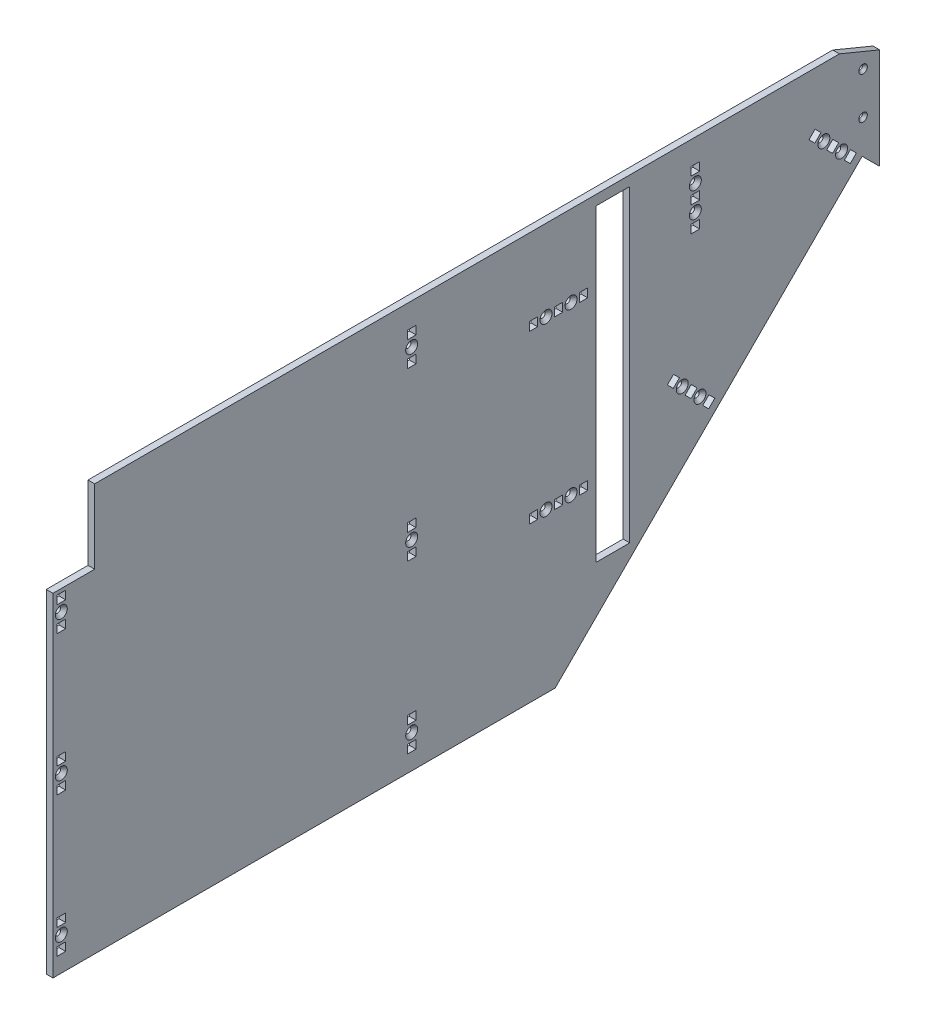
SolidWorks part; units mm, degrees
material "Delrin 2700 NC010, Low Viscosity Acetal Copolymer (SS)"
ref_plane "Front Plane" through (0, 0, 0) normal (0, 0, 1) x (1, 0, 0)
ref_plane "Top Plane" through (0, 0, 0) normal (0, 1, 0) x (1, 0, 0)
ref_plane "Right Plane" through (0, 0, 0) normal (1, 0, 0) x (0, 0, -1)
sketch "Sketch1" plane through (0, 0, 0) normal (1, 0, 0) x (0, 0, -1)
  line L0 (307.975, 0) -> (307.975, -76.2) construction
  line L1 (-307.975, 0) -> (307.975, 0)
  line L2 (-307.975, 0) -> (-307.975, -309.88)
  line L3 (-307.975, -309.88) -> (74.295, -309.88)
  line L4 (101.6, -254) -> (-228.6, -254) construction
  line L5 (105.41, -7.62) -> (131.064, -7.62)
  line L6 (105.41, -7.62) -> (105.41, -242.57)
  line L7 (307.975, -76.2) -> (74.295, -309.88)
  line L8 (105.41, -242.57) -> (131.064, -242.57)
  line L9 (131.064, -7.62) -> (131.064, -242.57)
  line L10 (101.6, -254) -> (101.6, 0) construction
  line L11 (-228.6, -254) -> (-228.6, 0) construction
  line L12 (-307.975, -5.08) -> (307.975, -5.08) construction
  line L13 (101.6, -254) -> (130.175, -254) construction
  line L14 (307.975, -76.2) -> (307.975, -289.8019) construction
  line L15 (307.975, -76.2) -> (321.3376, -89.5626)
  line L17 (321.3376, -89.5626) -> (321.3376, 0)
  line L18 (321.3376, 0) -> (307.975, 0)
  point P0 (0, 0)
  dimension "D1" = 234.95
  dimension "D2" = 25.654
  dimension "D3" = 45
  dimension "D4" = 304.8
  dimension "D5" = 254
  dimension "D6" = 76.2
  dimension "D7" = 330.2
  dimension "D8" = 5.08
  dimension "D9" = 2.54
  dimension "D10" = 3.81
  dimension "D11" = 79.375
  dimension "D12" = 615.95
  dimension "D13" = 251.4472
  dimension "D14" = 18.8976
  dimension "D15" = 7.4536
extrude "Boss-Extrude1" add sketch "Sketch1" along normal blind 5.08
sketch "Sketch2" plane through (5.08, 0, 0) normal (1, 0, 0) x (0, 0, -1)
  line L1 (-307.975, 0) -> (-276.225, 0)
  line L2 (-307.975, 0) -> (-307.975, -56.261)
  line L3 (-307.975, -56.261) -> (-276.225, -56.261)
  line L4 (-276.225, 0) -> (-276.225, -56.261)
  dimension "D1" = 31.75
  dimension "D2" = 56.261
extrude "Cut-Extrude1" cut sketch "Sketch2" against normal through all
chamfer "Chamfer1" distance 12.7 angle 67.5 1 edges at (2.54, 0, -321.3376)
sketch "Sketch4" plane through (5.08, 0, 0) normal (1, 0, 0) x (0, 0, -1)
  line L6 (307.975, -76.2) -> (321.3376, -89.5626) construction
  line L7 (74.295, -309.88) -> (307.975, -76.2) construction
  line B0 (285.6142, -53.8392) -> (290.1043, -58.3293)
  line B1 (290.1043, -58.3293) -> (285.4346, -62.999)
  line B2 (285.4346, -62.999) -> (280.9444, -58.5089)
  line B3 (280.9444, -58.5089) -> (285.6142, -53.8392)
  line B4 (272.1438, -40.3688) -> (276.6339, -44.8589)
  line B5 (276.6339, -44.8589) -> (271.9642, -49.5286)
  line B6 (271.9642, -49.5286) -> (267.474, -45.0385)
  line B7 (267.474, -45.0385) -> (272.1438, -40.3688)
  circle B8 centre (278.7892, -51.6839) radius 2.1526
  line B9 (299.0845, -67.3095) -> (303.5747, -71.7997)
  line B10 (299.0845, -67.3095) -> (294.4148, -71.9793)
  line B11 (294.4148, -71.9793) -> (298.9049, -76.4694)
  line B12 (303.5747, -71.7997) -> (298.9049, -76.4694)
  circle B13 centre (292.2596, -65.1543) radius 2.1527
  line B14 (177.8511, -161.6022) -> (182.3412, -166.0924)
  line B15 (182.3412, -166.0924) -> (177.6715, -170.7621)
  line B16 (177.6715, -170.7621) -> (173.1814, -166.272)
  line B17 (173.1814, -166.272) -> (177.8511, -161.6022)
  line B18 (164.3807, -148.1319) -> (168.8708, -152.622)
  line B19 (168.8708, -152.622) -> (164.2011, -157.2917)
  line B20 (164.2011, -157.2917) -> (159.711, -152.8016)
  line B21 (159.711, -152.8016) -> (164.3807, -148.1319)
  circle B22 centre (171.0261, -159.447) radius 2.1526
  line B23 (191.3215, -175.0726) -> (195.8116, -179.5627)
  line B24 (191.3215, -175.0726) -> (186.6517, -179.7424)
  line B25 (186.6517, -179.7424) -> (191.1419, -184.2325)
  line B26 (195.8116, -179.5627) -> (191.1419, -184.2325)
  circle B27 centre (184.4965, -172.9174) radius 2.1527
  dimension "D1" = 152.4
  dimension "D2" = 6.223
sketch_block_instance "BOLT_HOLE_2X-6"
sketch_block "BOLT_HOLE_2X" parameters "D1"=4.3053, "D2"=6.35, "D3"=6.35, "D4"=6.604, "D5"=19.05
sketch_block_instance "BOLT_HOLE_2X-7"
extrude "Cut-Extrude5" cut sketch "Sketch4" against normal through all
sketch "Sketch5" plane through (5.08, 0, 0) normal (1, 0, 0) x (0, 0, -1)
  line L0 (105.41, -7.62) -> (105.41, -242.57) construction
  line L3 (131.064, -7.62) -> (105.41, -7.62) construction
  line B0 (73.66, -58.42) -> (80.01, -58.42)
  line B1 (80.01, -58.42) -> (80.01, -65.024)
  line B2 (80.01, -65.024) -> (73.66, -65.024)
  line B3 (73.66, -65.024) -> (73.66, -58.42)
  line B4 (54.61, -58.42) -> (60.96, -58.42)
  line B5 (60.96, -58.42) -> (60.96, -65.024)
  line B6 (60.96, -65.024) -> (54.61, -65.024)
  line B7 (54.61, -65.024) -> (54.61, -58.42)
  circle B8 centre (67.31, -61.722) radius 2.1526
  line B9 (67.31, -61.722) -> (60.96, -61.722) construction
  line B10 (67.31, -61.722) -> (73.66, -61.722) construction
  line B11 (80.01, -61.722) -> (86.36, -61.722) construction
  line B12 (92.71, -58.42) -> (99.06, -58.42)
  line B13 (92.71, -58.42) -> (92.71, -65.024)
  line B14 (92.71, -65.024) -> (99.06, -65.024)
  line B15 (99.06, -58.42) -> (99.06, -65.024)
  line B16 (86.36, -61.722) -> (92.71, -61.722) construction
  circle B17 centre (86.36, -61.722) radius 2.1527
  line B18 (73.66, -185.42) -> (80.01, -185.42)
  line B19 (80.01, -185.42) -> (80.01, -192.024)
  line B20 (80.01, -192.024) -> (73.66, -192.024)
  line B21 (73.66, -192.024) -> (73.66, -185.42)
  line B22 (54.61, -185.42) -> (60.96, -185.42)
  line B23 (60.96, -185.42) -> (60.96, -192.024)
  line B24 (60.96, -192.024) -> (54.61, -192.024)
  line B25 (54.61, -192.024) -> (54.61, -185.42)
  circle B26 centre (67.31, -188.722) radius 2.1526
  line B27 (67.31, -188.722) -> (60.96, -188.722) construction
  line B28 (67.31, -188.722) -> (73.66, -188.722) construction
  line B29 (80.01, -188.722) -> (86.36, -188.722) construction
  line B30 (92.71, -185.42) -> (99.06, -185.42)
  line B31 (92.71, -185.42) -> (92.71, -192.024)
  line B32 (92.71, -192.024) -> (99.06, -192.024)
  line B33 (99.06, -185.42) -> (99.06, -192.024)
  line B34 (86.36, -188.722) -> (92.71, -188.722) construction
  circle B35 centre (86.36, -188.722) radius 2.1527
  dimension "D1" = 6.35
  dimension "D2" = 50.8
  dimension "D3" = 127
sketch_block_instance "BOLT_HOLE_2X-1"
sketch_block_instance "BOLT_HOLE_2X-2"
extrude "Cut-Extrude6" cut sketch "Sketch5" against normal through all
sketch "Sketch6" plane through (5.08, 0, 0) normal (1, 0, 0) x (0, 0, -1)
  line L0 (-301.625, -71.755) -> (-301.625, -178.1175) construction
  line L1 (-301.625, -178.1175) -> (-301.625, -284.48) construction
  line L2 (-34.925, -30.48) -> (-34.925, -157.48) construction
  line L3 (-34.925, -157.48) -> (-34.925, -284.48) construction
  line L4 (-307.975, -309.88) -> (74.295, -309.88) construction
  line L5 (-307.975, -56.261) -> (-307.975, -309.88) construction
  line L7 (290.6771, 0) -> (-276.225, 0) construction
  line B0 (184.277, -36.83) -> (184.277, -43.18)
  line B1 (184.277, -43.18) -> (177.673, -43.18)
  line B2 (177.673, -43.18) -> (177.673, -36.83)
  line B3 (177.673, -36.83) -> (184.277, -36.83)
  line B4 (184.277, -17.78) -> (184.277, -24.13)
  line B5 (184.277, -24.13) -> (177.673, -24.13)
  line B6 (177.673, -24.13) -> (177.673, -17.78)
  line B7 (177.673, -17.78) -> (184.277, -17.78)
  circle B8 centre (180.975, -30.48) radius 2.1526
  line B9 (180.975, -30.48) -> (180.975, -24.13) construction
  line B10 (180.975, -30.48) -> (180.975, -36.83) construction
  line B11 (180.975, -43.18) -> (180.975, -49.53) construction
  line B12 (184.277, -55.88) -> (184.277, -62.23)
  line B13 (184.277, -55.88) -> (177.673, -55.88)
  line B14 (177.673, -55.88) -> (177.673, -62.23)
  line B15 (184.277, -62.23) -> (177.673, -62.23)
  line B16 (180.975, -49.53) -> (180.975, -55.88) construction
  circle B17 centre (180.975, -49.53) radius 2.1527
  line B18 (-31.623, -290.83) -> (-31.623, -297.18)
  line B19 (-31.623, -297.18) -> (-38.227, -297.18)
  line B20 (-38.227, -297.18) -> (-38.227, -290.83)
  line B21 (-38.227, -290.83) -> (-31.623, -290.83)
  line B22 (-31.623, -271.78) -> (-31.623, -278.13)
  line B23 (-31.623, -278.13) -> (-38.227, -278.13)
  line B24 (-38.227, -278.13) -> (-38.227, -271.78)
  line B25 (-38.227, -271.78) -> (-31.623, -271.78)
  circle B26 centre (-34.925, -284.48) radius 2.1526
  line B27 (-34.925, -284.48) -> (-34.925, -278.13) construction
  line B28 (-34.925, -284.48) -> (-34.925, -290.83) construction
  line B29 (-31.623, -36.83) -> (-31.623, -43.18)
  line B30 (-31.623, -43.18) -> (-38.227, -43.18)
  line B31 (-38.227, -43.18) -> (-38.227, -36.83)
  line B32 (-38.227, -36.83) -> (-31.623, -36.83)
  line B33 (-31.623, -17.78) -> (-31.623, -24.13)
  line B34 (-31.623, -24.13) -> (-38.227, -24.13)
  line B35 (-38.227, -24.13) -> (-38.227, -17.78)
  line B36 (-38.227, -17.78) -> (-31.623, -17.78)
  circle B37 centre (-34.925, -30.48) radius 2.1526
  line B38 (-34.925, -30.48) -> (-34.925, -24.13) construction
  line B39 (-34.925, -30.48) -> (-34.925, -36.83) construction
  line B40 (-38.227, -151.13) -> (-38.227, -144.78)
  line B41 (-38.227, -144.78) -> (-31.623, -144.78)
  line B42 (-31.623, -144.78) -> (-31.623, -151.13)
  line B43 (-31.623, -151.13) -> (-38.227, -151.13)
  line B44 (-38.227, -170.18) -> (-38.227, -163.83)
  line B45 (-38.227, -163.83) -> (-31.623, -163.83)
  line B46 (-31.623, -163.83) -> (-31.623, -170.18)
  line B47 (-31.623, -170.18) -> (-38.227, -170.18)
  circle B48 centre (-34.925, -157.48) radius 2.1526
  line B49 (-34.925, -157.48) -> (-34.925, -163.83) construction
  line B50 (-34.925, -157.48) -> (-34.925, -151.13) construction
  line B51 (-304.927, -65.405) -> (-304.927, -59.055)
  line B52 (-304.927, -59.055) -> (-298.323, -59.055)
  line B53 (-298.323, -59.055) -> (-298.323, -65.405)
  line B54 (-298.323, -65.405) -> (-304.927, -65.405)
  line B55 (-304.927, -84.455) -> (-304.927, -78.105)
  line B56 (-304.927, -78.105) -> (-298.323, -78.105)
  line B57 (-298.323, -78.105) -> (-298.323, -84.455)
  line B58 (-298.323, -84.455) -> (-304.927, -84.455)
  circle B59 centre (-301.625, -71.755) radius 2.1526
  line B60 (-301.625, -71.755) -> (-301.625, -78.105) construction
  line B61 (-301.625, -71.755) -> (-301.625, -65.405) construction
  line B62 (-304.927, -171.7675) -> (-304.927, -165.4175)
  line B63 (-304.927, -165.4175) -> (-298.323, -165.4175)
  line B64 (-298.323, -165.4175) -> (-298.323, -171.7675)
  line B65 (-298.323, -171.7675) -> (-304.927, -171.7675)
  line B66 (-304.927, -190.8175) -> (-304.927, -184.4675)
  line B67 (-304.927, -184.4675) -> (-298.323, -184.4675)
  line B68 (-298.323, -184.4675) -> (-298.323, -190.8175)
  line B69 (-298.323, -190.8175) -> (-304.927, -190.8175)
  circle B70 centre (-301.625, -178.1175) radius 2.1526
  line B71 (-301.625, -178.1175) -> (-301.625, -184.4675) construction
  line B72 (-301.625, -178.1175) -> (-301.625, -171.7675) construction
  line B73 (-304.927, -278.13) -> (-304.927, -271.78)
  line B74 (-304.927, -271.78) -> (-298.323, -271.78)
  line B75 (-298.323, -271.78) -> (-298.323, -278.13)
  line B76 (-298.323, -278.13) -> (-304.927, -278.13)
  line B77 (-304.927, -297.18) -> (-304.927, -290.83)
  line B78 (-304.927, -290.83) -> (-298.323, -290.83)
  line B79 (-298.323, -290.83) -> (-298.323, -297.18)
  line B80 (-298.323, -297.18) -> (-304.927, -297.18)
  circle B81 centre (-301.625, -284.48) radius 2.1526
  line B82 (-301.625, -284.48) -> (-301.625, -290.83) construction
  line B83 (-301.625, -284.48) -> (-301.625, -278.13) construction
  dimension "D1" = 266.7
  dimension "D2" = 59.055
  dimension "D3" = 12.7
  dimension "D4" = 6.35
  dimension "D6" = 17.78
  dimension "D7" = 215.9
sketch_block_instance "BOLT_HOLE_2X-4"
sketch_block_instance "BOLT_HOLE-6"
sketch_block "BOLT_HOLE" parameters "D1"=4.3053, "D2"=6.35, "D3"=6.35, "D4"=6.604
sketch_block_instance "BOLT_HOLE-7"
sketch_block_instance "BOLT_HOLE-8"
sketch_block_instance "BOLT_HOLE-9"
sketch_block_instance "BOLT_HOLE-10"
sketch_block_instance "BOLT_HOLE-11"
extrude "Cut-Extrude7" cut sketch "Sketch6" against normal through all
hole_wizard "CSK for #8 Flat Head Socket Cap Screw2" positions "Sketch10" profile "Sketch9" countersink size "#8" standard "ANSI Inch" end condition through all
sketch "Sketch10" plane through (5.08, 0, 0) normal (1, 0, 0) x (0, 0, -1)
  circle A0 centre (86.36, -61.722) radius 2.1527 construction
  point P0 (-301.625, -71.755)
  point P3 (-301.625, -178.1175)
  point P6 (-301.625, -284.48)
  point P9 (-34.925, -284.48)
  point P12 (-34.925, -157.48)
  point P15 (-34.925, -30.48)
  point P18 (180.975, -30.48)
  point P21 (180.975, -49.53)
  point P24 (278.7892, -51.6839)
  point P27 (292.2596, -65.1543)
  point P30 (171.0261, -159.447)
  point P33 (184.4965, -172.9174)
  point P36 (67.31, -188.722)
  point P39 (86.36, -188.722)
  point P42 (67.31, -61.722)
  point P45 (86.36, -61.722)
sketch "Sketch9" plane through (5.08, -71.755, 301.625) normal (0, 1, 0) x (0, 0, -1)
  line L0 (0, 0) -> (0, 5.08)
  line L1 (0, 5.08) -> (2.1526, 5.08)
  line L2 (2.1526, 5.08) -> (2.1526, 2.7685)
  line L3 (2.1526, 2.7685) -> (4.5593, 0)
  line L5 (4.5593, 0) -> (0, 0)
  line L6 (-2.1526, 2.7685) -> (-4.5593, 0) construction
  line L11 (0, -6.35) -> (0, 107.95) construction
  dimension "Thru Hole Dia." = 4.3053
  dimension "Thru Hole Depth" = 5.08
  dimension "Near C'Sink Dia." = 9.1186
  dimension "Near C'Sink Angle" = 82
sketch "Sketch11" [suppressed] plane through (5.08, 0, 0) normal (1, 0, 0) x (0, 0, -1)
  line L0 (290.6771, 0) -> (-276.225, 0) construction
  line L1 (-307.975, -309.88) -> (79.375, -309.88)
  line L2 (-307.975, -309.88) -> (-307.975, -304.8)
  line L3 (-307.975, -304.8) -> (79.375, -304.8)
  line L4 (79.375, -309.88) -> (79.375, -304.8)
  line L5 (74.295, -309.88) -> (307.975, -76.2) construction
  line L6 (-307.975, -56.261) -> (-307.975, -309.88) construction
  line L7 (-307.975, -309.88) -> (74.295, -309.88) construction
  dimension "D1" = 304.8
extrude "Cut-Extrude8" [suppressed] cut sketch "Sketch11" against normal through all
other "Move Face1" [suppressed] parameters "D1"=0.0508
hole_wizard "CSK for #4 Flat Head Socket Cap Screw1" positions "Sketch13" profile "Sketch12" countersink size "#4" standard "ANSI Inch" end condition through all
sketch "Sketch13" plane through (5.08, 0, 0) normal (1, 0, 0) x (0, 0, -1)
  line L0 (308.6376, -19.05) -> (308.6376, -50.8) construction
  line L2 (321.3376, -89.5626) -> (321.3376, -12.7) construction
  point P0 (308.6376, -19.05)
  point P2 (308.6376, -50.8)
  dimension "D1" = 12.7
  dimension "D2" = 6.35
  dimension "D3" = 31.75
sketch "Sketch12" plane through (5.08, -19.05, -308.6376) normal (0, 1, 0) x (0, 0, -1)
  line L0 (0, 0) -> (0, 5.08)
  line L1 (0, 5.08) -> (1.4732, 5.08)
  line L2 (1.4732, 5.08) -> (1.4732, 2.0307)
  line L3 (1.4732, 2.0307) -> (3.2385, 0)
  line L5 (3.2385, 0) -> (0, 0)
  line L6 (-1.4732, 2.0307) -> (-3.2385, 0) construction
  line L11 (0, -6.35) -> (0, 107.95) construction
  dimension "Thru Hole Dia." = 2.9464
  dimension "Thru Hole Depth" = 5.08
  dimension "Near C'Sink Dia." = 6.477
  dimension "Near C'Sink Angle" = 82
